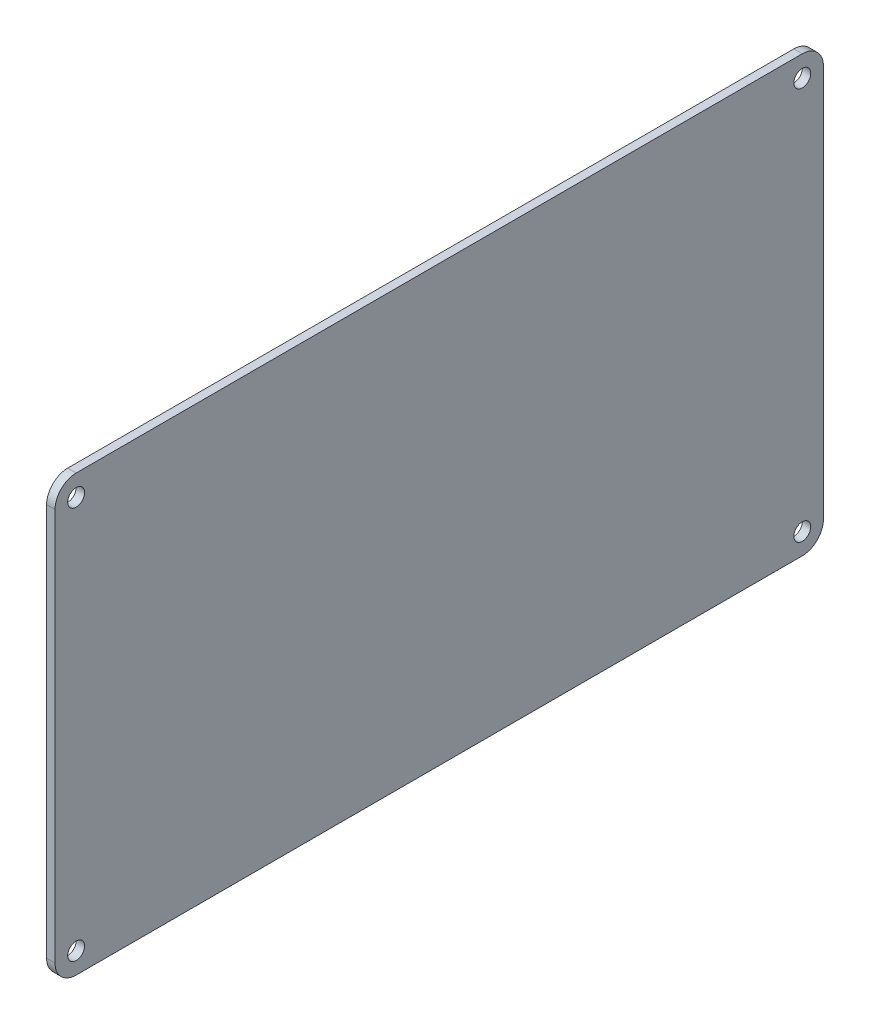
SolidWorks part; units mm, degrees
ref_plane "Front Plane" through (0, 0, 0) normal (1, 0, 0) x (0, 1, 0)
ref_plane "Top Plane" through (0, 0, 0) normal (0, 0, 1) x (0, 1, 0)
ref_plane "Right Plane" through (0, 0, 0) normal (0, 1, 0) x (-1, 0, 0)
sketch "Sketch1" plane through (0, 0, 0) normal (0, 0, 1) x (0, 1, 0)
  line L1 (-8.8276, 0) -> (94.1724, 0)
  line L2 (-8.8276, 0) -> (-8.8276, 2)
  line L3 (-8.8276, 2) -> (94.1724, 2)
  line L4 (94.1724, 0) -> (94.1724, 2)
  dimension "D1" = 2
  dimension "D2" = 103
extrude "Boss-Extrude1" add sketch "Sketch1" along normal blind 182
sketch "Sketch2" plane through (0, 0, 0) normal (1, 0, 0) x (0, 1, 0)
  line L0 (-8.8276, 182) -> (94.1724, 182) construction
  line L1 (-8.8276, 182) -> (-8.8276, 0) construction
  line L2 (94.1724, 182) -> (94.1724, 0) construction
  line L3 (-8.8276, 0) -> (94.1724, 0) construction
  circle A0 centre (-3.8276, 177) radius 2
  circle A1 centre (89.1724, 177) radius 2
  circle A2 centre (89.1724, 5) radius 2
  circle A3 centre (-3.8276, 5) radius 2
  dimension "D1" = 5
  dimension "D3" = 5
  dimension "D5" = 5
  dimension "D2" = 5
  dimension "D4" = 5
  dimension "D6" = 5
extrude "Cut-Extrude1" cut sketch "Sketch2" against normal blind 168
fillet "Fillet1" radius 5 1 edges at (-1, -8.8276, 182)
fillet "Fillet2" radius 5 1 edges at (-1, 94.1724, 182)
fillet "Fillet3" radius 5 1 edges at (-1, 94.1724, 0)
fillet "Fillet4" radius 5 1 edges at (-1, -8.8276, 0)
